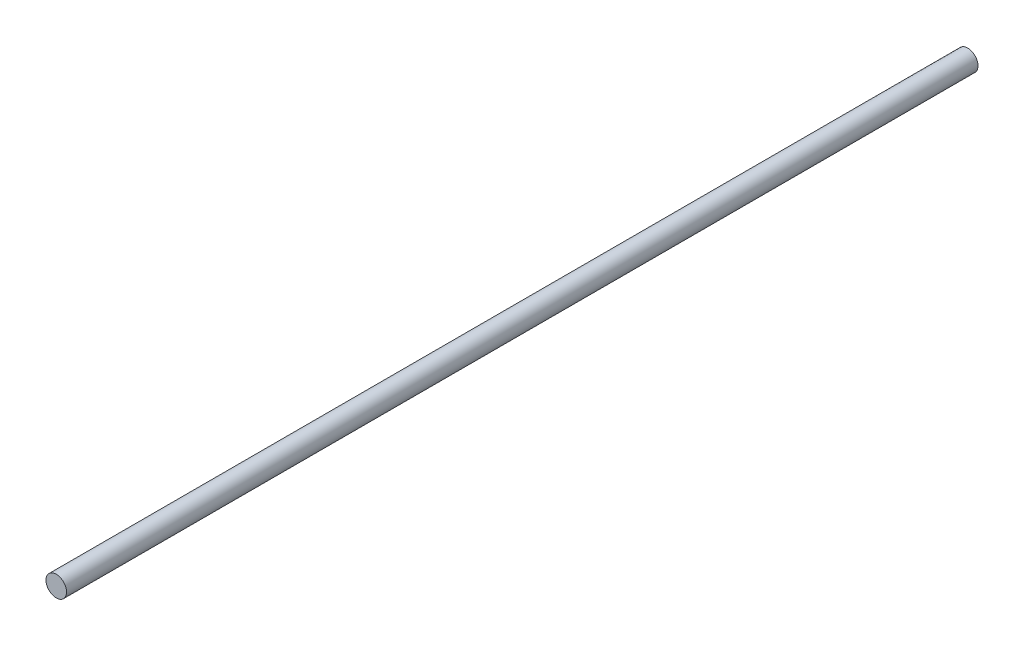
SolidWorks part; units mm, degrees
ref_plane "Ön Düzlem" through (0, 0, 0) normal (0, 0, 1) x (1, 0, 0)
ref_plane "Üst Düzlem" through (0, 0, 0) normal (0, 1, 0) x (1, 0, 0)
ref_plane "Sağ Düzlem" through (0, 0, 0) normal (1, 0, 0) x (0, 0, -1)
sketch "Çizim1" plane through (0, 0, 0) normal (0, 0, 1) x (1, 0, 0)
  circle A0 centre (0, 0) radius 6
  dimension "D1" = 12
extrude "Yükseklik-Ekstrüzyon1" add sketch "Çizim1" along normal blind 532
